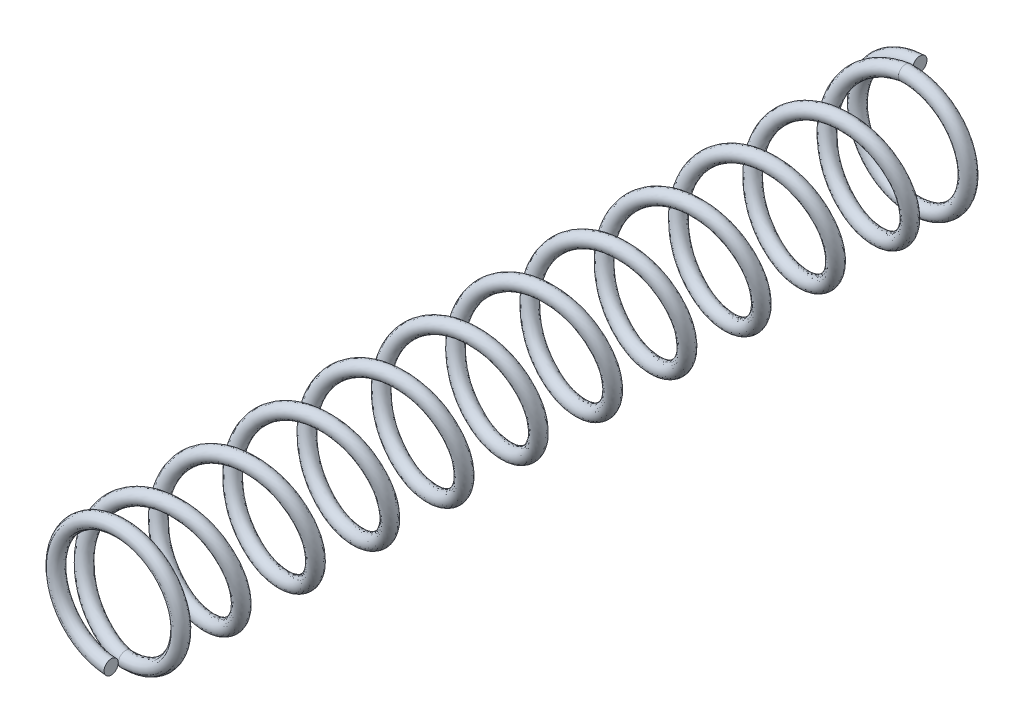
SolidWorks part; units mm, degrees
ref_plane "Front" through (0, 0, 0) normal (0, 0, 1) x (1, 0, 0)
ref_plane "Top" through (0, 0, 0) normal (0, 1, 0) x (1, 0, 0)
ref_plane "Right" through (0, 0, 0) normal (1, 0, 0) x (0, 0, -1)
sketch "Sketch1" plane through (0, 0, 0) normal (0, 0, 1) x (1, 0, 0)
  circle A0 centre (0, 0) radius 1.0541
  dimension "D1" = 2.1082
curve "Helix/Spiral1" pitch 1.331 height 13.9751 turns 10.5
sketch "Sketch4" plane through (0, 0, 0) normal (0, 0, 1) x (1, 0, 0)
  circle A0 centre (0, 0) radius 1.0541
  dimension "D1" = 2.1082
curve "Helix/Spiral2" pitch 0.2565 height 0.2565 turns 1
ref_plane "Plane1" through (0, 0, 13.9751) normal (0, 0, 1) x (1, 0, 0)
sketch "Sketch5" plane through (0, 0, 13.9751) normal (0, 0, 1) x (1, 0, 0)
  circle A0 centre (0, 0) radius 1.0541
curve "Helix/Spiral3" pitch 0.2565 height 0.2565 turns 1
sketch "Sketch6" plane through (0, 0, 0) normal (1, 0, 0) x (0, 0, -1)
  circle A0 centre (0.2565, 1.0541) radius 0.127
  spline S0 degree 3 poles (0, 1.0541) (0.0053, 1.0541) (0.016, 0.9992) (0.0321, 0.7648) (0.0481, 0.4139) (0.0641, 0) (0.0802, -0.4139) (0.0962, -0.7648) (0.1122, -0.9992) (0.1283, -1.0815) (0.1443, -0.9992) (0.1603, -0.7648) (0.1764, -0.4139) (0.1924, 0) (0.2084, 0.4139) (0.2245, 0.7648) (0.2405, 0.9992) (0.2512, 1.0541) (0.2565, 1.0541) knots 0 0 0 0 0.0625 0.125 0.1875 0.25 0.3125 0.375 0.4375 0.5 0.5625 0.625 0.6875 0.75 0.8125 0.875 0.9375 1 1 1 1 construction
  dimension "D1" = 0.254
  dimension "D2" = 1.0541
sweep "Sweep1" add profiles "Sketch6" path "Helix/Spiral2"
sketch "Sketch7" plane through (0, 0, 0) normal (-1, 0, 0) x (0, 0, 1)
  circle A0 centre (0, 1.0541) radius 0.127
  circle A1 centre (0, 1.0541) radius 0.127 construction
sweep "Sweep2" add profiles "Sketch7" path "Helix/Spiral1"
sketch "Sketch8" plane through (0, 0, 0) normal (1, 0, 0) x (0, 0, -1)
  circle A0 centre (-13.9751, -1.0541) radius 0.127
  circle A1 centre (-13.9751, -1.0541) radius 0.127 construction
  spline S0 degree 3 poles (-13.9751, -1.0541) (-13.9804, -1.0541) (-13.9911, -0.9992) (-14.0071, -0.7648) (-14.0232, -0.4139) (-14.0392, 0) (-14.0552, 0.4139) (-14.0713, 0.7648) (-14.0873, 0.9992) (-14.1033, 1.0815) (-14.1194, 0.9992) (-14.1354, 0.7648) (-14.1515, 0.4139) (-14.1675, 0) (-14.1835, -0.4139) (-14.1996, -0.7648) (-14.2156, -0.9992) (-14.2263, -1.0541) (-14.2316, -1.0541) knots 0 0 0 0 0.0625 0.125 0.1875 0.25 0.3125 0.375 0.4375 0.5 0.5625 0.625 0.6875 0.75 0.8125 0.875 0.9375 1 1 1 1 construction
sweep "Sweep3" add profiles "Sketch8" path "Helix/Spiral3"
